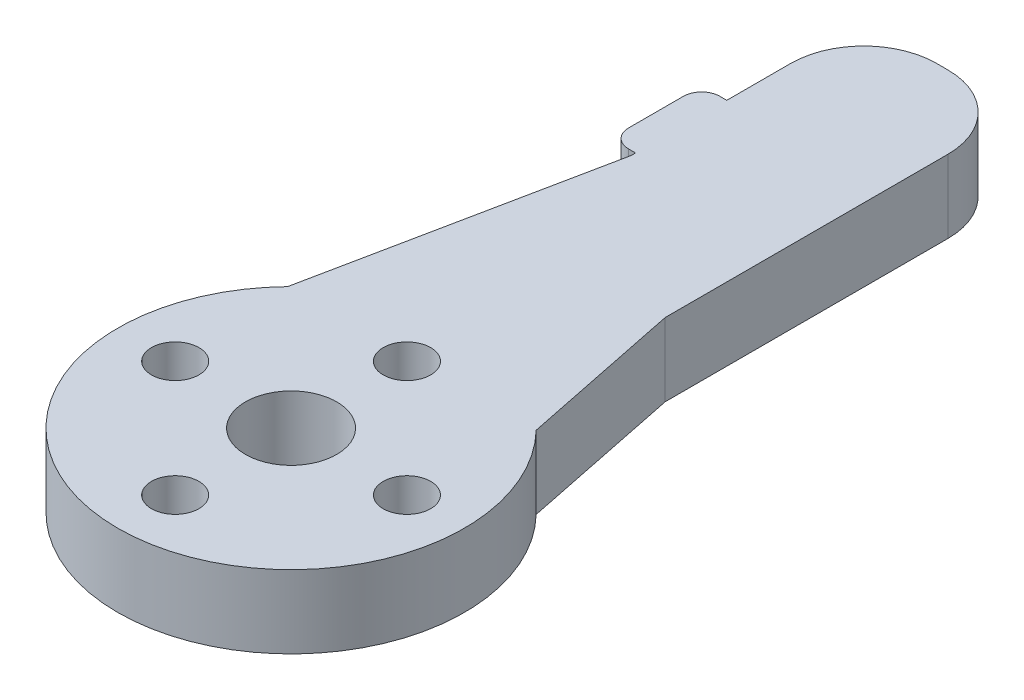
SolidWorks part; units mm, degrees
material "Tough 2000"
ref_plane "Front Plane" through (0, 0, 0) normal (0, 0, 1) x (1, 0, 0)
ref_plane "Top Plane" through (0, 0, 0) normal (0, 1, 0) x (1, 0, 0)
ref_plane "Right Plane" through (0, 0, 0) normal (1, 0, 0) x (0, 0, -1)
sketch "Sketch1" plane through (0, 0, 0) normal (0, 1, 0) x (1, 0, 0)
  line L1 (-4.5316, 17.7996) -> (-7.8384, 1.6)
  line L2 (4.5316, 17.7996) -> (7.8384, 1.6)
  arc A0 (-7.8384, 1.6) -> (7.8384, 1.6) centre (0, 0) ccw
  arc A1 (4.5316, 17.7996) -> (-4.5316, 17.7996) centre (0, 16.8746) ccw
  circle A2 centre (0, 16.8746) radius 3
  circle A3 centre (0, 0) radius 2.5
extrude "Boss-Extrude1" add sketch "Sketch1" along normal blind 4
sketch "Sketch2" plane through (0, 4, 0) normal (0, 1, 0) x (1, 0, 0)
  line L0 (0, 0) -> (0, 6.35) construction
  circle A0 centre (0, 6.35) radius 1.3
  circle A1 centre (6.35, 0) radius 1.3
  circle A2 centre (0, -6.35) radius 1.3
  circle A3 centre (-6.35, 0) radius 1.3
  point P13 (0, 0)
  dimension "D1" = 4
extrude "Cut-Extrude1" cut sketch "Sketch2" against normal blind 4
sketch "Sketch3" plane through (0, 4, 0) normal (0, 1, 0) x (1, 0, 0)
  line L0 (-7.8384, 1.6) -> (-6.8137, 6.62)
  line L1 (6.8137, 6.62) -> (7.8384, 1.6)
  line L2 (7.8384, 1.6) -> (4.5316, 17.7996) construction
  arc A1 (-6.8137, 6.62) -> (6.8137, 6.62) centre (0, 0) ccw
  arc A2 (-7.8384, 1.6) -> (7.8384, 1.6) centre (0, 0) ccw construction
  arc A3 (-7.8384, 1.6) -> (7.8384, 1.6) centre (0, 0) ccw
extrude "Boss-Extrude2" add sketch "Sketch3" against normal blind 4
sketch "Sketch4" plane through (0, 4, 0) normal (0, 1, 0) x (1, 0, 0)
  line L0 (0, 0) -> (0, 10)
  line L1 (0, 35) -> (5, 35)
  line L2 (5, 35) -> (5, 10)
  line L3 (0, 35) -> (-5, 35)
  line L4 (-5, 35) -> (-5, 10)
  line L5 (-5, 10) -> (5, 10)
  line M4 (-4.5316, 17.7996) -> (-6.8137, 6.62)
  line M6 (6.8137, 6.62) -> (4.5316, 17.7996)
  arc M7 (4.5316, 17.7996) -> (-4.5316, 17.7996) centre (0, 16.8746) ccw
  circle M12 centre (0, 16.8746) radius 3
extrude "Boss-Extrude3" add sketch "Sketch4" against normal blind 4 contours L3 L4 L2 L1 M4 M7 M6 | M12 | L4 L5 L2 M6 M7 M4 M12
sketch "Sketch6" plane through (0, 0, 0) normal (0, -1, 0) x (1, 0, 0)
  line L0 (-6.8137, -6.62) -> (-3.6205, -22.2635)
  line L1 (-3.6205, -22.2635) -> (-3.6205, -22.5)
  line L2 (-3.6205, -22.5) -> (-5, -22.5)
  line L3 (-5, -35) -> (-5, -15.5051) construction
  line L4 (-5, -22.5) -> (-5, -27.5)
  line L5 (-5, -27.5) -> (-3.6205, -27.5)
  line L6 (-3.6205, -27.5) -> (-3.6205, -35)
  line L7 (5, -35) -> (-5, -35) construction
  line L8 (-3.6205, -35) -> (-5, -35)
  line L9 (-5, -35) -> (-5, -27.5)
  line L10 (-5, -22.5) -> (-5, -15.5051)
  line L11 (-5, -15.5051) -> (-5, -22.5)
  line L12 (-5, -15.5051) -> (-5, -22.5)
  line M1 (-5, -15.5051) -> (-5, -35)
  line M3 (-5, -35) -> (5, -35)
  dimension "D1" = 5
  dimension "D2" = 7.5
extrude "Cut-Extrude2" cut sketch "Sketch6" against normal blind 9 contours L6 L5 M1 M3 | L2 L1 L0 M1
fillet "Fillet3" radius 4 2 edges at (-3.6205, 2, -35) (5, 2, -35)
fillet "Fillet4" radius 1 2 edges at (-5, 2, -22.5) (-5, 2, -27.5)
